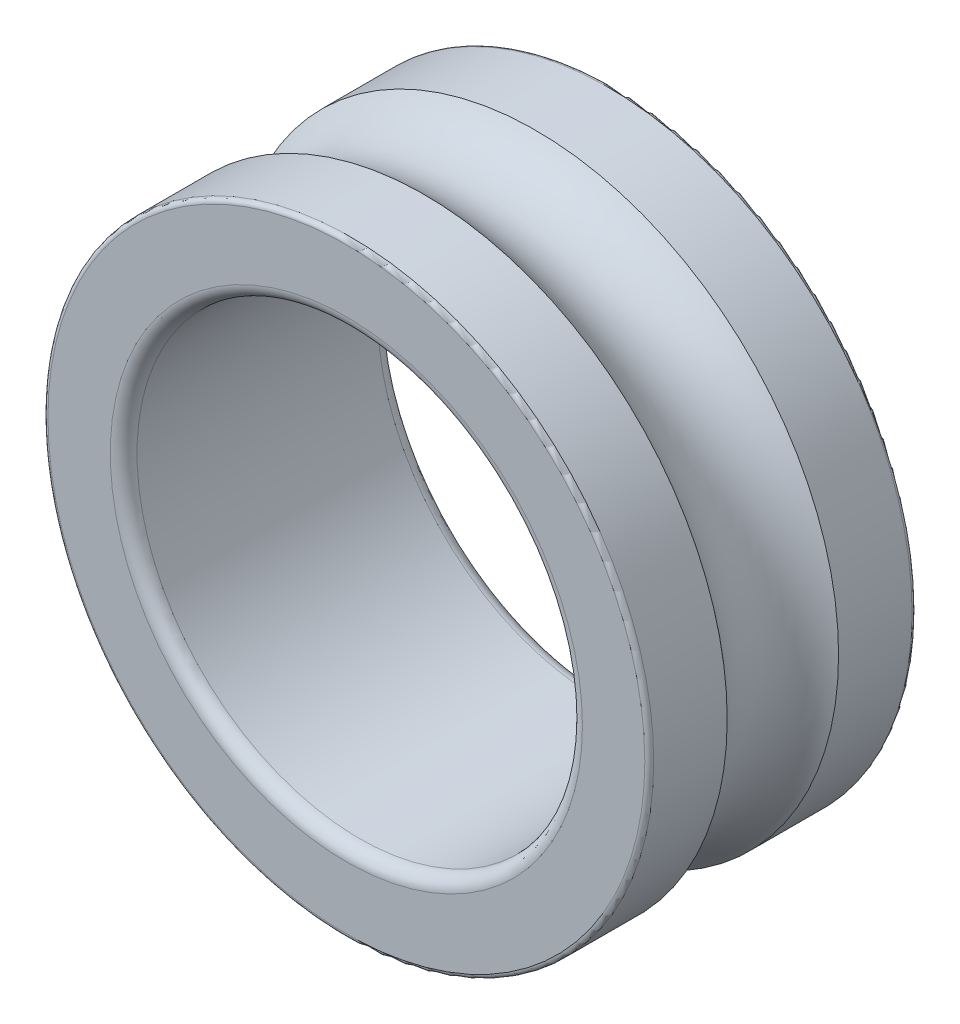
SolidWorks part; units mm, degrees
ref_plane "Front Plane" through (0, 0, 0) normal (0, 0, 1) x (1, 0, 0)
ref_plane "Top Plane" through (0, 0, 0) normal (0, 1, 0) x (1, 0, 0)
ref_plane "Right Plane" through (0, 0, 0) normal (1, 0, 0) x (0, 0, -1)
sketch "Sketch2" plane through (0, 0, 0) normal (1, 0, 0) x (0, 0, -1)
  line L1 (-6, -6.75) -> (6, -6.75) construction
  line L3 (-6, 6.85) -> (-2.5, 6.85)
  line L7 (2.5, 6.85) -> (6, 6.85)
  line L9 (-2.5, 6.85) -> (-2.5, 3.25)
  line L10 (-2.5, -6.75) -> (2.5, -6.75)
  line L11 (2.5, 6.85) -> (2.5, 3.25)
  line L14 (-6, -6.75) -> (6, -6.75)
  line L16 (-6, 3.25) -> (6, 3.25)
  line L18 (-6, 3.25) -> (-6, 6.85)
  line L19 (6, 3.25) -> (6, 6.85)
  arc A0 (-2.5, 6.85) -> (2.5, 6.85) centre (0, 8.8475) ccw
  point P0 (0, 0)
  point P7 (0, 0)
  point P10 (0, 0)
  dimension "D4" = 6.4
  dimension "D2" = 13.6
  dimension "D3" = 5
  dimension "D5" = 10
revolve "Revolve1" add sketch "Sketch2" angle 360 about L14
fillet "Fillet1" radius 0.2 2 edges at (13.6, -6.75, -6) (13.6, -6.75, 6)
fillet "Fillet2" radius 0.6 2 edges at (10, -6.75, -6) (10, -6.75, 6)
